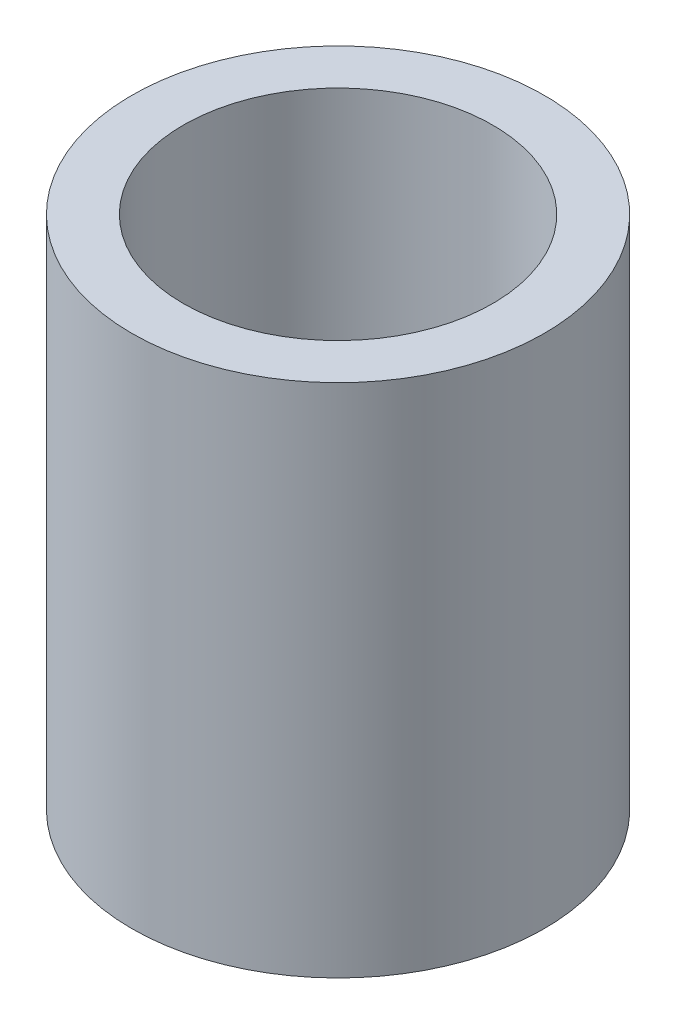
SolidWorks part; units mm, degrees
ref_plane "前视基准面" through (0, 0, 0) normal (0, 0, 1) x (1, 0, 0)
ref_plane "上视基准面" through (0, 0, 0) normal (0, 1, 0) x (1, 0, 0)
ref_plane "右视基准面" through (0, 0, 0) normal (1, 0, 0) x (0, 0, -1)
sketch "草图1" plane through (0, 0, 0) normal (0, 1, 0) x (1, 0, 0)
  circle A0 centre (0, 0) radius 2
  circle A1 centre (0, 0) radius 1.5
  dimension "D1" = 3
  dimension "D2" = 4
extrude "凸台-拉伸1" add sketch "草图1" along normal blind 5
